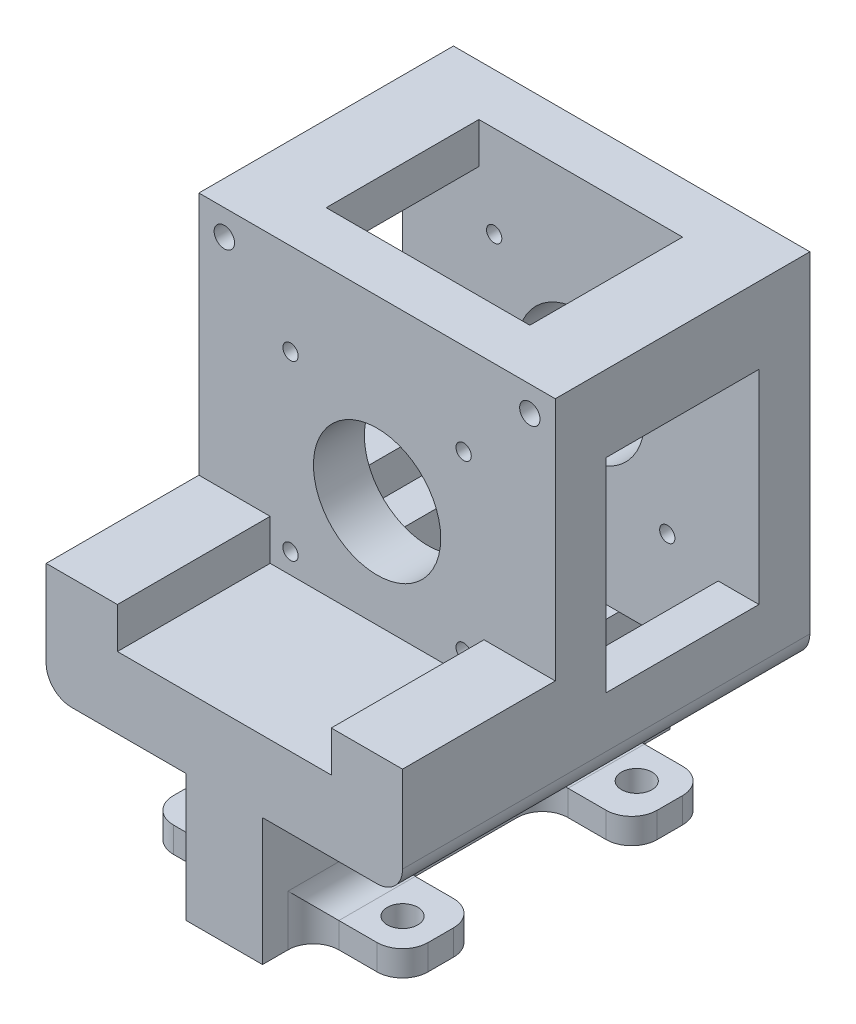
SolidWorks part; units mm, degrees
ref_plane "Front Plane" through (0, 0, 0) normal (0, 0, 1) x (1, 0, 0)
ref_plane "Top Plane" through (0, 0, 0) normal (0, 1, 0) x (1, 0, 0)
ref_plane "Right Plane" through (0, 0, 0) normal (1, 0, 0) x (0, 0, -1)
sketch "Sketch1" plane through (0, 0, 0) normal (0, 0, 1) x (1, 0, 0)
  line L0 (-100, -60) -> (100, -60) construction
  line L1 (-17, -17) -> (17, -17) construction
  line L2 (-17, -17) -> (-17, 17) construction
  line L3 (-17, 17) -> (17, 17) construction
  line L4 (17, -17) -> (17, 17) construction
  line L5 (-17, -17) -> (17, 17) construction
  line L6 (-17, 17) -> (17, -17) construction
  line L7 (-100, -60) -> (-41.6228, 27.7046) construction
  line L8 (100, -60) -> (41.6228, 27.7046) construction
  line L9 (35, -35) -> (35, 35)
  line L10 (-35, 35) -> (35, 35)
  line L11 (-35, -35) -> (-35, 35)
  line L12 (-35, -35) -> (35, -35)
  circle A0 centre (0, 0) radius 50 construction
  circle A1 centre (0, 0) radius 12.5
  circle A2 centre (17, 17) radius 1.5
  circle A3 centre (-17, 17) radius 1.5
  circle A4 centre (17, -17) radius 1.5
  circle A5 centre (-17, -17) radius 1.5
  point P0 (0, 0)
  point P11 (0, -60)
  dimension "D3" = 100
  dimension "D7" = 25
  dimension "D8" = 3
  dimension "D1" = 34
  dimension "D2" = 34
  dimension "D4" = 60
  dimension "D5" = 200
  dimension "D6" = 18
extrude "Boss-Extrude1" add sketch "Sketch1" along normal blind 10
sketch "Sketch2" plane through (0, 0, 10) normal (0, 0, 1) x (1, 0, 0)
  line L0 (-21, -13) -> (-21, -21)
  line L1 (-21, -21) -> (21, -21) construction
  line L2 (-21, -21) -> (-21, 21) construction
  line L3 (-21, 21) -> (21, 21) construction
  line L4 (21, -21) -> (21, 21) construction
  line L5 (-21, -21) -> (21, 21) construction
  line L6 (-21, 21) -> (21, -21) construction
  line L7 (-21, -21) -> (21, -21)
  line L8 (21, -21) -> (21, -13)
  line L9 (21, -13) -> (35, -13)
  line L10 (35, -35) -> (35, 35) construction
  line L11 (35, -13) -> (35, -35)
  line L12 (35, -35) -> (-35, -35)
  line L13 (-35, -35) -> (-35, -13)
  line L14 (-35, -35) -> (-35, 35) construction
  line L15 (-35, -13) -> (-21, -13)
  point P0 (0, 0)
  dimension "D1" = 42
  dimension "D2" = 42
  dimension "D3" = 22
  dimension "D4" = 22
extrude "Boss-Extrude2" add sketch "Sketch2" along normal blind 30
sketch "Sketch3" plane through (0, 0, 0) normal (0, 0, -1) x (-1, 0, 0)
  line L0 (27, 20) -> (35, 20)
  line L3 (20, 35) -> (35, 35)
  line L4 (35, 20) -> (35, 35)
  line L9 (20, 27) -> (27, 27)
  line L10 (27, 20) -> (27, 27)
  line L13 (20, 27) -> (20, 35)
  line L14 (27, 27) -> (35, 35) construction
  point P0 (0, 0)
  point P7 (0, 0)
  dimension "D1" = 8
  dimension "D2" = 15
extrude "Boss-Extrude3" add sketch "Sketch3" along normal blind 30
pattern_circular "CirPattern1" count 4 over 360 about axis through (0, 0, 0) along (0, 0, 1) of "Boss-Extrude3"
ref_plane "Plane1" through (0, 0, -15) normal (0, 0, -1) x (-1, 0, 0)
mirror "Mirror1" about plane through (0, 0, -15) normal (0, 0, -1) of "Boss-Extrude1"
sketch "Sketch4" plane through (0, 0, -40) normal (0, 0, -1) x (-1, 0, 0)
  line L0 (17, 17) -> (-17, -17) construction
  line L1 (-35, -35) -> (35, -35) construction
  line L2 (-35, -35) -> (-35, 35) construction
  line L3 (-35, 35) -> (35, 35) construction
  line L4 (35, -35) -> (35, 35) construction
  line L5 (-35, -35) -> (35, 35) construction
  line L6 (-35, 35) -> (35, -35) construction
  line L8 (-30, -30) -> (30, -30) construction
  line L9 (-30, -30) -> (-30, 30) construction
  line L10 (-30, 30) -> (30, 30) construction
  line L11 (30, -30) -> (30, 30) construction
  line L12 (-30, -30) -> (30, 30) construction
  line L13 (-30, 30) -> (30, -30) construction
  circle A1 centre (30, 30) radius 2
  point P0 (0, 0)
  point P9 (0, 0)
  dimension "D1" = 5
  dimension "D2" = 4
extrude "Cut-Extrude1" cut sketch "Sketch4" against normal up to next (50 mm away)
mirror "Mirror2" about plane through (0, 0, 0) normal (1, 0, 0) of "Cut-Extrude1"
sketch "Sketch6" plane through (0, -35, 0) normal (0, -1, 0) x (1, 0, 0)
  line L0 (-35, 0) -> (35, 0) construction
  line L1 (-7.5, -40) -> (7.5, -40)
  line L2 (-7.5, -40) -> (-7.5, 40)
  line L3 (-7.5, 40) -> (7.5, 40)
  line L4 (7.5, -40) -> (7.5, 40)
  line L5 (-7.5, -40) -> (7.5, 40) construction
  line L6 (-7.5, 40) -> (7.5, -40) construction
  line L7 (-35, 40) -> (35, 40) construction
  point P0 (0, 0)
  dimension "D1" = 15
extrude "Boss-Extrude4" add sketch "Sketch6" along normal blind 25
sketch "Sketch7" plane through (0, -60, 0) normal (0, -1, 0) x (1, 0, 0)
  line L0 (-7.5, -40) -> (7.5, -40) construction
  line L1 (-25, 15) -> (25, 15)
  line L2 (-25, 15) -> (-25, 30)
  line L3 (-25, 30) -> (25, 30)
  line L4 (25, 15) -> (25, 30)
  line L5 (-25, 15) -> (25, 30) construction
  line L6 (-25, 30) -> (25, 15) construction
  line L7 (-25, -15) -> (25, -15)
  line L8 (-25, -15) -> (-25, -30)
  line L9 (-25, -30) -> (25, -30)
  line L10 (25, -15) -> (25, -30)
  line L11 (-25, -15) -> (25, -30) construction
  line L12 (-25, -30) -> (25, -15) construction
  line L13 (7.5, 40) -> (-7.5, 40) construction
  point P0 (0, 22.5)
  point P5 (0, -22.5)
  point P10 (0, 0)
  point P13 (0, -40)
  point P14 (0, -30)
  dimension "D1" = 50
  dimension "D2" = 15
  dimension "D3" = 50
  dimension "D4" = 15
  dimension "D5" = 10
  dimension "D6" = 10
extrude "Boss-Extrude5" add sketch "Sketch7" against normal blind 5
sketch "Sketch8" plane through (0, -60, 0) normal (0, -1, 0) x (1, 0, 0)
  line L0 (25, 15) -> (25, 30) construction
  line L1 (-18, 23) -> (18, 23) construction
  line L2 (-18, 23) -> (-18, -23) construction
  line L3 (-18, -23) -> (18, -23) construction
  line L4 (18, 23) -> (18, -23) construction
  line L5 (-25, 30) -> (-25, 15) construction
  line L6 (25, 30) -> (7.5, 30) construction
  line L7 (7.5, -30) -> (25, -30) construction
  point P12 (16.25, -30)
  dimension "D1" = 7
  dimension "D2" = 7
  dimension "D3" = 7
  dimension "D4" = 7
hole_wizard "Ø6.0mm Dowel Hole1" positions "3DSketch1" profile "Sketch9" hole size "Ø6.0" standard "KS" end condition up to next
sketch3d "3DSketch1"
  point P0 (-18, -60, 23)
  point P3 (18, -60, 23)
  point P6 (-18, -60, -23)
  point P9 (18, -60, -23)
sketch "Sketch9" plane through (-18, -60, 23) normal (1, 0, 0) x (0, 0, -1)
  line L0 (0, 0) -> (0, 5)
  line L1 (0, 5) -> (3, 5)
  line L2 (3, 5) -> (3, 0)
  line L5 (3, 0) -> (0, 0)
  line L11 (0, -6.35) -> (0, 107.95) construction
  dimension "Thru Hole Dia." = 6
  dimension "Thru Hole Depth" = 5
fillet "Fillet1" radius 5 16 edges at (7.5, -57.5, -30) (7.5, -57.5, 15) (25, -57.5, 15) (25, -57.5, -30) (25, -57.5, -15) (25, -57.5, 30) (7.5, -57.5, -15) (7.5, -57.5, 30) (-7.5, -57.5, 15) (-7.5, -57.5, 30) (-7.5, -57.5, -15) (-25, -57.5, 30) (-25, -57.5, 15) (-25, -57.5, -15) (-25, -57.5, -30) (-7.5, -57.5, -30)
fillet "Fillet2" radius 5 4 edges at (-7.5, -55, 22.5) (-7.5, -55, -22.5) (7.5, -55, -22.5) (7.5, -55, 22.5)
fillet "Fillet3" radius 5 2 edges at (-35, -35, 0) (35, -35, 0)
